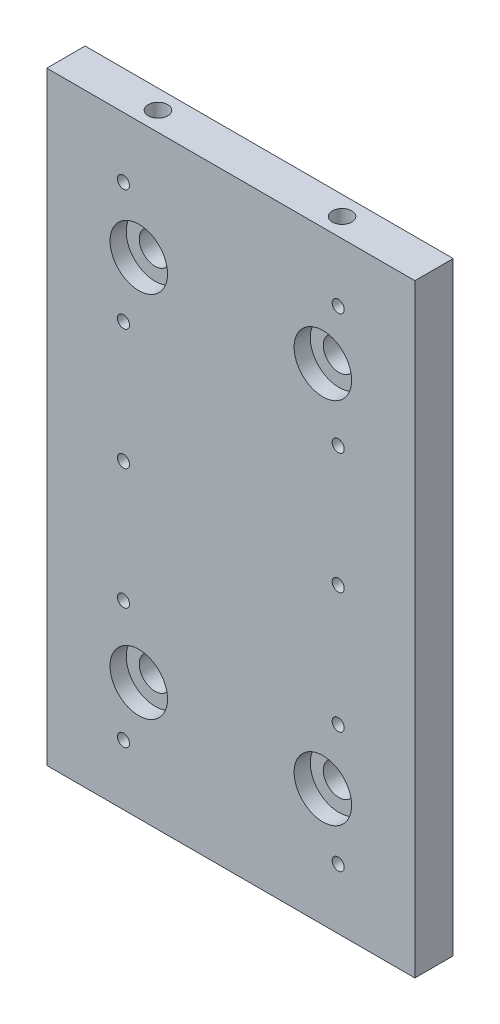
SolidWorks part; units mm, degrees
material "6061-T6 (SS)"
ref_plane "Front Plane" through (0, 0, 0) normal (0, 0, 1) x (1, 0, 0)
ref_plane "Top Plane" through (0, 0, 0) normal (0, 1, 0) x (1, 0, 0)
ref_plane "Right Plane" through (0, 0, 0) normal (1, 0, 0) x (0, 0, -1)
sketch "Sketch1" plane through (0, 0, 0) normal (0, 0, 1) x (1, 0, 0)
  line L1 (-38.1, 62.5) -> (38.1, 62.5)
  line L2 (-38.1, 62.5) -> (-38.1, -62.5)
  line L3 (-38.1, -62.5) -> (38.1, -62.5)
  line L4 (38.1, 62.5) -> (38.1, -62.5)
  line L5 (-38.1, 62.5) -> (38.1, -62.5) construction
  line L6 (-38.1, -62.5) -> (38.1, 62.5) construction
  point P0 (0, 0)
  dimension "D1" = 76.2
  dimension "D2" = 125
extrude "Boss-Extrude1" add sketch "Sketch1" along normal blind 7.9375
hole_wizard "CBORE for 1/4 Button Head Cap Screw1" positions "Sketch3" profile "Sketch2" counterbore size "1/4" standard "ANSI Inch" end condition up to next
sketch "Sketch3" plane through (0, 0, 7.9375) normal (0, 0, 1) x (1, 0, 0)
  line L0 (-19.05, 38.1) -> (19.05, 38.1) construction
  line L1 (0, 38.1) -> (0, 0) construction
  line L2 (19.05, 38.1) -> (19.05, -38.1) construction
  line L3 (19.05, -38.1) -> (-19.05, -38.1) construction
  line L4 (-19.05, -38.1) -> (-19.05, 38.1) construction
  line L5 (19.05, 0) -> (0, 0) construction
  point P0 (-19.05, 38.1)
  point P2 (19.05, 38.1)
  point P4 (19.05, -38.1)
  point P6 (-19.05, -38.1)
  dimension "D1" = 38.1
  dimension "D2" = 76.2
sketch "Sketch2" plane through (-19.05, 38.1, 7.9375) normal (1, 0, 0) x (0, -1, 0)
  line L0 (0, 0) -> (0, 7.9375)
  line L1 (0, 7.9375) -> (3.2639, 7.9375)
  line L3 (3.2639, 7.9375) -> (3.2639, 3.3528)
  line L4 (3.2639, 3.3528) -> (5.9538, 3.3528)
  line L5 (5.9538, 3.3528) -> (5.9538, 0)
  line L7 (5.9538, 0) -> (0, 0)
  line L11 (0, -6.35) -> (0, 107.95) construction
  dimension "Thru Hole Dia." = 6.5278
  dimension "Thru Hole Depth" = 7.9375
  dimension "C'Bore Dia." = 11.9075
  dimension "C'Bore Depth" = 3.3528
hole_wizard "M3x0.5 Tapped Hole1" positions "Sketch5" profile "Sketch4" tap size "M3x0.5" standard "ANSI Metric" end condition up to next
sketch "Sketch5" plane through (0, 0, 7.9375) normal (0, 0, 1) x (1, 0, 0)
  line L0 (22.225, 50) -> (22.225, -50) construction
  line L1 (-22.225, 50) -> (-22.225, -50) construction
  line L2 (22.225, 0) -> (-22.225, 0) construction
  line L3 (-22.225, -25) -> (22.225, -25) construction
  line L4 (-22.225, -50) -> (22.225, -50) construction
  line L5 (-22.225, 25) -> (22.225, 25) construction
  line L6 (-22.225, 50) -> (22.225, 50) construction
  point P0 (-22.225, 50)
  point P2 (-22.225, 25)
  point P4 (-22.225, 0)
  point P6 (-22.225, -25)
  point P8 (-22.225, -50)
  point P10 (22.225, -50)
  point P12 (22.225, -25)
  point P14 (22.225, 0)
  point P16 (22.225, 25)
  point P18 (22.225, 50)
  dimension "D1" = 44.45
  dimension "D2" = 25
  dimension "D3" = 25
  dimension "D4" = 25
  dimension "D5" = 25
sketch "Sketch4" plane through (-22.225, 50, 7.9375) normal (1, 0, 0) x (0, -1, 0)
  line L0 (0, 0) -> (0, 7.9375)
  line L1 (0, 7.9375) -> (1.25, 7.9375)
  line L2 (1.25, 7.9375) -> (1.25, 0)
  line L5 (1.25, 0) -> (0, 0)
  line L11 (0, -6.35) -> (0, 107.95) construction
  dimension "Thread Major Dia." = 2.5
  dimension "Thru Tap Drill Depth" = 7.9375
hole_wizard "#10-32 Tapped Hole1" positions "Sketch7" profile "Sketch6" tap size "#10-32" standard "ANSI Inch"
sketch "Sketch7" plane through (0, 62.5, 0) normal (0, 1, 0) x (1, 0, 0)
  line L0 (-19.05, -3.9688) -> (19.05, -3.9688) construction
  line L1 (0, -3.9688) -> (0, 0) construction
  line L2 (19.05, -3.9688) -> (38.1, -3.9688) construction
  line L3 (38.1, -7.9375) -> (38.1, 0) construction
  point P0 (-19.05, -3.9688)
  point P2 (19.05, -3.9688)
  dimension "D1" = 38.1
sketch "Sketch6" plane through (-19.05, 62.5, 3.9688) normal (1, 0, 0) x (0, 0, 1)
  line L0 (0, 0) -> (0, 11.3733)
  line L1 (0, 11.3733) -> (2.0193, 10.16)
  line L2 (2.0193, 10.16) -> (2.0193, 0)
  line L5 (2.0193, 0) -> (0, 0)
  line L10 (0, 11.3733) -> (-2.0193, 10.16) construction
  line L11 (0, -6.35) -> (0, 107.95) construction
  dimension "Tap Drill Dia." = 4.0386
  dimension "Tap Drill Depth" = 10.16
  dimension "Drill Angle" = 118
hole_wizard "#10-32 Tapped Hole2" positions "Sketch9" profile "Sketch8" tap size "#10-32" standard "ANSI Inch"
sketch "Sketch9" plane through (0, -62.5, 0) normal (0, -1, 0) x (-1, 0, 0)
  point P0 (19.05, -3.9688)
  point P3 (-19.05, -3.9688)
sketch "Sketch8" plane through (-19.05, -62.5, 3.9688) normal (1, 0, 0) x (0, 0, -1)
  line L0 (0, 0) -> (0, 11.3733)
  line L1 (0, 11.3733) -> (2.0193, 10.16)
  line L2 (2.0193, 10.16) -> (2.0193, 0)
  line L5 (2.0193, 0) -> (0, 0)
  line L10 (0, 11.3733) -> (-2.0193, 10.16) construction
  line L11 (0, -6.35) -> (0, 107.95) construction
  dimension "Tap Drill Dia." = 4.0386
  dimension "Tap Drill Depth" = 10.16
  dimension "Drill Angle" = 118
sketch "Sketch10" plane through (0, 0, 0) normal (0, 0, -1) x (-1, 0, 0)
  line L0 (-30.1625, 55.5625) -> (-30.1625, -55.5625) construction
  line L1 (7.9375, -60.325) -> (-7.9375, -60.325)
  line L2 (12.7, -55.5625) -> (12.7, 55.5625)
  line L3 (7.9375, 60.325) -> (-7.9375, 60.325)
  line L4 (-12.7, -55.5625) -> (-12.7, 55.5625)
  line L5 (12.7, -60.325) -> (-12.7, 60.325) construction
  line L6 (12.7, 60.325) -> (-12.7, -60.325) construction
  line L7 (-25.4, 55.5625) -> (-25.4, -55.5625)
  line L8 (-34.925, 55.5625) -> (-34.925, -55.5625)
  line L9 (30.1625, 55.5625) -> (30.1625, -55.5625) construction
  line L10 (34.925, 55.5625) -> (34.925, -55.5625)
  line L11 (25.4, 55.5625) -> (25.4, -55.5625)
  line L12 (30.1625, 0) -> (0, 0) construction
  line L13 (-30.1625, 0) -> (0, 0) construction
  arc A0 (-7.9375, -60.325) -> (-12.7, -55.5625) centre (-7.9375, -55.5625) cw
  arc A1 (7.9375, -60.325) -> (12.7, -55.5625) centre (7.9375, -55.5625) ccw
  arc A2 (12.7, 55.5625) -> (7.9375, 60.325) centre (7.9375, 55.5625) ccw
  arc A3 (-7.9375, 60.325) -> (-12.7, 55.5625) centre (-7.9375, 55.5625) ccw
  arc A4 (-25.4, 55.5625) -> (-34.925, 55.5625) centre (-30.1625, 55.5625) ccw
  arc A5 (-34.925, -55.5625) -> (-25.4, -55.5625) centre (-30.1625, -55.5625) ccw
  arc A6 (34.925, 55.5625) -> (25.4, 55.5625) centre (30.1625, 55.5625) ccw
  arc A7 (25.4, -55.5625) -> (34.925, -55.5625) centre (30.1625, -55.5625) ccw
  point P0 (0, 0)
  point P20 (-30.1625, 0)
  point P25 (30.1625, 0)
  dimension "D3" = 4.7625
  dimension "D8" = 4.7625
  dimension "D9" = 4.7625
  dimension "D1" = 120.65
  dimension "D2" = 25.4
  dimension "D4" = 30.1625
  dimension "D5" = 30.1625
  dimension "D6" = 111.125
  dimension "D7" = 111.125
extrude "Cut-Extrude1" cut sketch "Sketch10" against normal blind 4.7625
